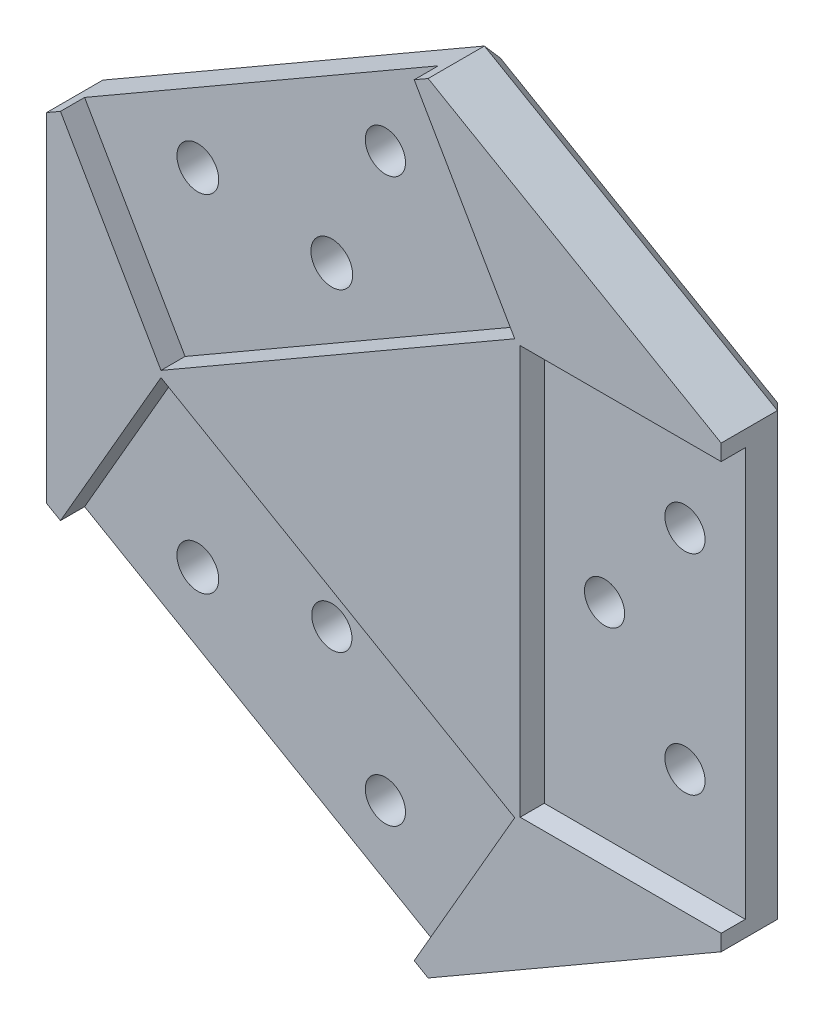
SolidWorks part; units mm, degrees
ref_plane "Front Plane" through (0, 0, 0) normal (0, 0, 1) x (1, 0, 0)
ref_plane "Top Plane" through (0, 0, 0) normal (0, 1, 0) x (1, 0, 0)
ref_plane "Right Plane" through (0, 0, 0) normal (1, 0, 0) x (0, 0, -1)
sketch "Sketch1" plane through (0, 0, 0) normal (0, 0, 1) x (1, 0, 0)
  line L0 (2973.461, 1234.0709) -> (2998.461, 1234.0709) construction
  line L1 (2990.961, 1247.0709) -> (2990.961, 1234.0709) construction
  line L2 (2990.961, 1234.0709) -> (2990.961, 1221.0709) construction
  line L4465 (2960.2842, 1281.5123) -> (2972.7842, 1259.8617)
  line L4466 (2916.2901, 1256.1123) -> (2928.7901, 1234.4617)
  line L4467 (2916.2901, 1256.1123) -> (2925.8157, 1239.6135)
  line L4468 (2960.2842, 1186.6295) -> (2972.7842, 1208.2801)
  line L4469 (2916.2901, 1212.0295) -> (2928.7901, 1233.6801)
  line L4470 (2973.461, 1259.4709) -> (2998.461, 1259.4709)
  line L4471 (2973.461, 1208.6709) -> (2998.461, 1208.6709)
  line L4472 (2928.7901, 1234.4617) -> (2972.7842, 1259.8617)
  line L4473 (2973.461, 1259.4709) -> (2973.461, 1208.6709)
  line L4474 (2928.7901, 1233.6801) -> (2972.7842, 1208.2801)
  line L4475 (2998.461, 1261.4709) -> (2998.461, 1206.6709)
  line L4476 (2914.5581, 1255.1123) -> (2962.0163, 1282.5123)
  line L4477 (2914.5581, 1213.0295) -> (2962.0163, 1185.6295)
  line L4478 (2914.5581, 1255.1123) -> (2914.5581, 1213.0295)
  line L4479 (2962.0163, 1282.5123) -> (2998.461, 1261.4709)
  line L4480 (2962.0163, 1185.6295) -> (2998.461, 1206.6709)
  circle A635 centre (2990.961, 1221.0709) radius 2.5
  circle A636 centre (2980.961, 1234.0709) radius 2.5
  circle A637 centre (2990.961, 1247.0709) radius 2.5
  circle A638 centre (2953.6997, 1269.0504) radius 2.5
  circle A639 centre (2930.3747, 1255.5838) radius 2.6
  circle A640 centre (2947.0372, 1214.4849) radius 2.5
  circle A641 centre (2953.6997, 1199.0914) radius 2.5
  circle A642 centre (2930.3747, 1212.558) radius 2.6
  circle A1442 centre (2947.0372, 1253.6569) radius 2.6
  dimension "D1" = 26
  dimension "D3" = 50.8
  dimension "D4" = 10
extrude "Boss-Extrude1" add sketch "Sketch1" along normal blind 6
sketch "Sketch2" plane through (0, 0, 6) normal (0, 0, 1) x (1, 0, 0)
  line L0 (2928.7901, 1233.6801) -> (2972.7842, 1208.2801)
  line L17 (2962.0163, 1185.6295) -> (2998.461, 1206.6709) construction
  line L18 (2998.461, 1261.4709) -> (2998.461, 1206.6709) construction
  line L19 (2962.0163, 1282.5123) -> (2998.461, 1261.4709) construction
  line L20 (2914.5581, 1255.1123) -> (2962.0163, 1282.5123) construction
  line L21 (2914.5581, 1255.1123) -> (2914.5581, 1213.0295) construction
  line L25 (2960.2842, 1281.5123) -> (2972.7842, 1259.8617) construction
  line L26 (2928.7901, 1234.4617) -> (2972.7842, 1259.8617) construction
  line L28 (2916.2901, 1256.1123) -> (2925.8157, 1239.6135) construction
  line L29 (2973.461, 1259.4709) -> (2998.461, 1259.4709) construction
  line L30 (2973.461, 1259.4709) -> (2973.461, 1208.6709) construction
  line L31 (2973.461, 1208.6709) -> (2998.461, 1208.6709) construction
  line L33 (2962.0163, 1185.6295) -> (2998.461, 1206.6709)
  line L34 (2998.461, 1261.4709) -> (2998.461, 1206.6709)
  line L35 (2962.0163, 1282.5123) -> (2998.461, 1261.4709)
  line L36 (2914.5581, 1255.1123) -> (2962.0163, 1282.5123)
  line L37 (2914.5581, 1255.1123) -> (2914.5581, 1213.0295)
  line L38 (2972.7842, 1208.2801) -> (2960.2842, 1186.6295)
  line L40 (2928.7901, 1233.6801) -> (2916.2901, 1212.0295)
  line L41 (2960.2842, 1281.5123) -> (2972.7842, 1259.8617)
  line L42 (2928.7901, 1234.4617) -> (2972.7842, 1259.8617)
  line L43 (2914.5581, 1213.0295) -> (2962.0163, 1185.6295)
  line L44 (2916.2901, 1256.1123) -> (2928.7901, 1234.4617)
  line L45 (2973.461, 1259.4709) -> (2998.461, 1259.4709)
  line L46 (2973.461, 1259.4709) -> (2973.461, 1208.6709)
  line L47 (2973.461, 1208.6709) -> (2998.461, 1208.6709)
  circle A15 centre (2947.0372, 1253.6569) radius 2.6 construction
  circle A16 centre (2990.961, 1247.0709) radius 2.5 construction
  circle A17 centre (2980.961, 1234.0709) radius 2.5 construction
  circle A18 centre (2990.961, 1221.0709) radius 2.5 construction
  circle A19 centre (2930.3747, 1212.558) radius 2.6 construction
  circle A20 centre (2953.6997, 1199.0914) radius 2.5 construction
  circle A21 centre (2947.0372, 1214.4849) radius 2.5 construction
  circle A22 centre (2930.3747, 1255.5838) radius 2.6 construction
  circle A23 centre (2953.6997, 1269.0504) radius 2.5 construction
  circle A24 centre (2947.0372, 1253.6569) radius 2.6
  circle A25 centre (2990.961, 1247.0709) radius 2.5
  circle A26 centre (2980.961, 1234.0709) radius 2.5
  circle A27 centre (2990.961, 1221.0709) radius 2.5
  circle A28 centre (2930.3747, 1212.558) radius 2.6
  circle A29 centre (2953.6997, 1199.0914) radius 2.5
  circle A30 centre (2947.0372, 1214.4849) radius 2.5
  circle A31 centre (2930.3747, 1255.5838) radius 2.6
  circle A32 centre (2953.6997, 1269.0504) radius 2.5
  line M1 (2998.461, 1206.6709) -> (2998.461, 1261.4709)
  line M2 (2998.461, 1261.4709) -> (2962.0163, 1282.5123)
  line M3 (2962.0163, 1282.5123) -> (2914.5581, 1255.1123)
  line M4 (2914.5581, 1255.1123) -> (2914.5581, 1213.0295)
  line M5 (2914.5581, 1213.0295) -> (2962.0163, 1185.6295)
  line M6 (2962.0163, 1185.6295) -> (2998.461, 1206.6709)
extrude "Boss-Extrude2" add sketch "Sketch2" along normal blind 3 contours L47 L46 L45 L34 L41 L42 L44 L40 L0 L38 M2 M3 M4 M5 M6 M1
chamfer "Chamfer1" distance 2 angle 45 6 edges at (2938.2872, 1268.8123, 0) (2914.5581, 1234.0709, 0) (2938.2872, 1199.3295, 0) (2980.2387, 1196.1502, 0) (2998.461, 1234.0709, 0) (2980.2387, 1271.9916, 0)
